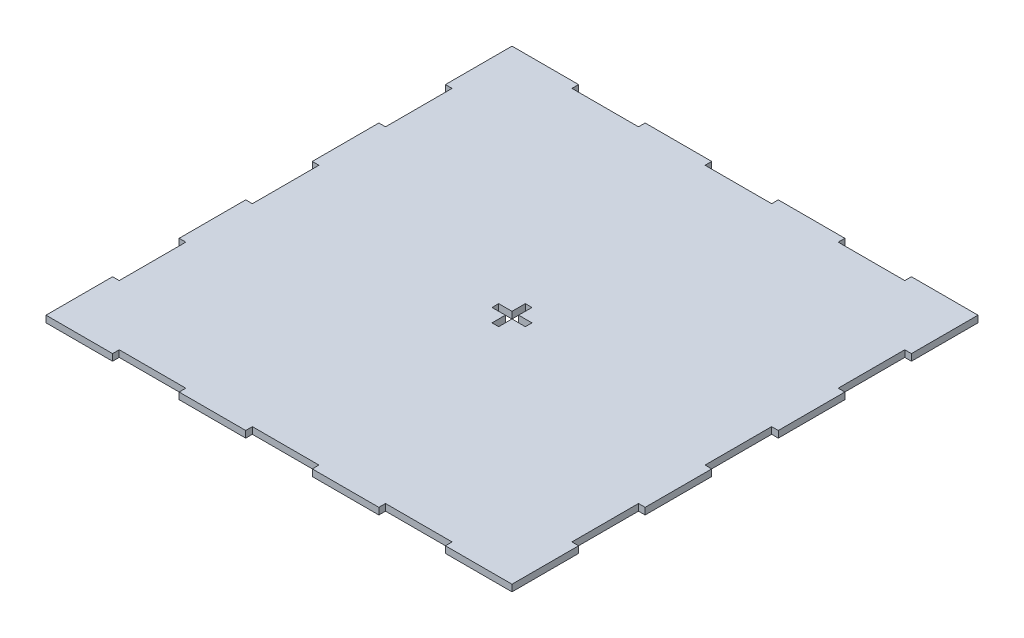
SolidWorks part; units mm, degrees
ref_plane "Front Plane" through (0, 0, 0) normal (0, 0, 1) x (1, 0, 0)
ref_plane "Top Plane" through (0, 0, 0) normal (0, 1, 0) x (1, 0, 0)
ref_plane "Right Plane" through (0, 0, 0) normal (1, 0, 0) x (0, 0, -1)
sketch "Sketch1" plane through (0, 0, 0) normal (0, 1, 0) x (1, 0, 0)
  line L7 (-210, -210) -> (210, -210)
  line L8 (-210, -210) -> (-210, 210)
  line L9 (-210, 210) -> (210, 210)
  line L10 (210, -210) -> (210, 210)
  line L11 (-210, -210) -> (210, 210) construction
  line L12 (-210, 210) -> (210, -210) construction
  point P0 (0, 0)
  dimension "D1" = 420
extrude "Boss-Extrude1" add sketch "Sketch1" along normal blind 6
sketch "Sketch2" plane through (0, 6, 0) normal (0, 1, 0) x (1, 0, 0)
  line L0 (60, 103.923) -> (40, 103.923)
  line L1 (120, 0) -> (60, 103.923) construction
  line L2 (60, 103.923) -> (-60, 103.923) construction
  line L3 (-60, 103.923) -> (-120, 0) construction
  line L4 (-120, 0) -> (-60, -103.923) construction
  line L5 (-60, -103.923) -> (60, -103.923) construction
  line L6 (60, -103.923) -> (120, 0) construction
  line L7 (116.5359, 0) -> (58.2679, 100.923) construction
  line L8 (58.2679, 100.923) -> (-58.2679, 100.923) construction
  line L9 (-58.2679, 100.923) -> (-116.5359, 0) construction
  line L10 (-116.5359, 0) -> (-58.2679, -100.923) construction
  line L11 (-58.2679, -100.923) -> (58.2679, -100.923) construction
  line L12 (58.2679, -100.923) -> (116.5359, 0) construction
  line L13 (40, 103.923) -> (40, 100.923)
  line L14 (40, 100.923) -> (58.2679, 100.923)
  line L15 (58.2679, 100.923) -> (67.4019, 85.1025)
  line L16 (67.4019, 85.1025) -> (70, 86.6025)
  line L17 (70, 86.6025) -> (60, 103.923)
  line L18 (110, -17.3205) -> (120, 0)
  line L19 (120, 0) -> (110, 17.3205)
  line L20 (110, 17.3205) -> (107.4019, 15.8205)
  line L21 (107.4019, 15.8205) -> (116.5359, 0)
  line L22 (116.5359, 0) -> (107.4019, -15.8205)
  line L23 (107.4019, -15.8205) -> (110, -17.3205)
  line L24 (40, -103.923) -> (60, -103.923)
  line L25 (60, -103.923) -> (70, -86.6025)
  line L26 (70, -86.6025) -> (67.4019, -85.1025)
  line L27 (67.4019, -85.1025) -> (58.2679, -100.923)
  line L28 (58.2679, -100.923) -> (40, -100.923)
  line L29 (40, -100.923) -> (40, -103.923)
  line L30 (-70, -86.6025) -> (-60, -103.923)
  line L31 (-60, -103.923) -> (-40, -103.923)
  line L32 (-40, -103.923) -> (-40, -100.923)
  line L33 (-40, -100.923) -> (-58.2679, -100.923)
  line L34 (-58.2679, -100.923) -> (-67.4019, -85.1025)
  line L35 (-67.4019, -85.1025) -> (-70, -86.6025)
  line L36 (-110, 17.3205) -> (-120, 0)
  line L37 (-120, 0) -> (-110, -17.3205)
  line L38 (-110, -17.3205) -> (-107.4019, -15.8205)
  line L39 (-107.4019, -15.8205) -> (-116.5359, 0)
  line L40 (-116.5359, 0) -> (-107.4019, 15.8205)
  line L41 (-107.4019, 15.8205) -> (-110, 17.3205)
  line L42 (-40, 103.923) -> (-60, 103.923)
  line L43 (-60, 103.923) -> (-70, 86.6025)
  line L44 (-70, 86.6025) -> (-67.4019, 85.1025)
  line L45 (-67.4019, 85.1025) -> (-58.2679, 100.923)
  line L46 (-58.2679, 100.923) -> (-40, 100.923)
  line L47 (-40, 100.923) -> (-40, 103.923)
  line L48 (0, 0) -> (130.1568, 75.1461) construction
  line L53 (76.75, 74.9112) -> (78.25, 72.3131)
  line L54 (76.75, 74.9112) -> (90.6757, 82.9512)
  line L55 (78.25, 72.3131) -> (92.1757, 80.3531)
  line L56 (90.6757, 82.9512) -> (92.1757, 80.3531)
  line L57 (74.1519, 73.4112) -> (75.6519, 70.8131)
  line L58 (74.1519, 73.4112) -> (47.3744, 57.9512)
  line L59 (75.6519, 70.8131) -> (48.8744, 55.3531)
  line L60 (47.3744, 57.9512) -> (48.8744, 55.3531)
  line L61 (101.75, 31.6099) -> (115.6757, 39.6499)
  line L62 (117.1757, 37.0519) -> (115.6757, 39.6499)
  line L63 (103.25, 29.0119) -> (117.1757, 37.0519)
  line L64 (103.25, 29.0119) -> (101.75, 31.6099)
  line L65 (99.1519, 30.1099) -> (72.3744, 14.6499)
  line L66 (73.8744, 12.0519) -> (72.3744, 14.6499)
  line L67 (100.6519, 27.5119) -> (73.8744, 12.0519)
  line L68 (100.6519, 27.5119) -> (99.1519, 30.1099)
  line L69 (26.5, -103.923) -> (23.5, -103.923)
  line L70 (26.5, -103.923) -> (26.5, -120.003)
  line L71 (26.5, -120.003) -> (23.5, -120.003)
  line L72 (23.5, -103.923) -> (23.5, -120.003)
  line L73 (26.5, -100.923) -> (23.5, -100.923)
  line L74 (26.5, -100.923) -> (26.5, -70.003)
  line L75 (26.5, -70.003) -> (23.5, -70.003)
  line L76 (23.5, -100.923) -> (23.5, -70.003)
  line L77 (-23.5, -103.923) -> (-23.5, -120.003)
  line L78 (-26.5, -120.003) -> (-23.5, -120.003)
  line L79 (-26.5, -103.923) -> (-26.5, -120.003)
  line L80 (-26.5, -103.923) -> (-23.5, -103.923)
  line L81 (-23.5, -100.923) -> (-23.5, -70.003)
  line L82 (-26.5, -70.003) -> (-23.5, -70.003)
  line L83 (-26.5, -100.923) -> (-26.5, -70.003)
  line L84 (-26.5, -100.923) -> (-23.5, -100.923)
  line L85 (-103.25, 29.0119) -> (-101.75, 31.6099)
  line L86 (-103.25, 29.0119) -> (-117.1757, 37.0519)
  line L87 (-117.1757, 37.0519) -> (-115.6757, 39.6499)
  line L88 (-101.75, 31.6099) -> (-115.6757, 39.6499)
  line L89 (-100.6519, 27.5119) -> (-99.1519, 30.1099)
  line L90 (-100.6519, 27.5119) -> (-73.8744, 12.0519)
  line L91 (-73.8744, 12.0519) -> (-72.3744, 14.6499)
  line L92 (-99.1519, 30.1099) -> (-72.3744, 14.6499)
  line L93 (-78.25, 72.3131) -> (-92.1757, 80.3531)
  line L94 (-90.6757, 82.9512) -> (-92.1757, 80.3531)
  line L95 (-76.75, 74.9112) -> (-90.6757, 82.9512)
  line L96 (-76.75, 74.9112) -> (-78.25, 72.3131)
  line L97 (-75.6519, 70.8131) -> (-48.8744, 55.3531)
  line L98 (-47.3744, 57.9512) -> (-48.8744, 55.3531)
  line L99 (-74.1519, 73.4112) -> (-47.3744, 57.9512)
  line L100 (-74.1519, 73.4112) -> (-75.6519, 70.8131)
  circle A0 centre (0, 0) radius 103.923 construction
  circle A1 centre (0, 0) radius 100.923 construction
  point P1 (90, 51.9615)
  point P52 (0, 0)
  point P69 (48.1244, 56.6522)
  point P104 (0, 0)
  dimension "D1" = 120
  dimension "D2" = 3
  dimension "D3" = 20
  dimension "D5" = 3
  dimension "D6" = 25
  dimension "D7" = 16.08
  dimension "D8" = 30.92
  dimension "D4" = 6
  dimension "D9" = 3
extrude "Cut-Extrude1" [suppressed] cut sketch "Sketch2" against normal through all
sketch "Sketch3" plane through (0, 6, 0) normal (0, 1, 0) x (1, 0, 0)
  line L7 (210, 210) -> (-210, 210) construction
  line L8 (-204, 204) -> (204, 204) construction
  line L9 (-204, 204) -> (-204, -204) construction
  line L10 (-204, -204) -> (204, -204) construction
  line L11 (204, 204) -> (204, -204) construction
  line L12 (-210, 210) -> (-210, -210) construction
  line L14 (-210, -210) -> (210, -210) construction
  line L16 (-204, 150) -> (-210, 150)
  line L17 (-204, 150) -> (-204, 90)
  line L18 (-204, 90) -> (-210, 90)
  line L19 (-210, 150) -> (-210, 90)
  line L105 (-204, 30) -> (-204, -30)
  line L106 (-204, 30) -> (-210, 30)
  line L107 (-210, 30) -> (-210, -30)
  line L108 (-204, -30) -> (-210, -30)
  line L109 (-204, -90) -> (-204, -150)
  line L110 (-204, -90) -> (-210, -90)
  line L111 (-210, -90) -> (-210, -150)
  line L112 (-204, -150) -> (-210, -150)
  line L113 (150, 204) -> (90, 204)
  line L114 (150, 204) -> (150, 210)
  line L115 (150, 210) -> (90, 210)
  line L116 (90, 204) -> (90, 210)
  line L117 (30, 204) -> (-30, 204)
  line L118 (-30, 204) -> (-30, 210)
  line L119 (30, 210) -> (-30, 210)
  line L120 (30, 204) -> (30, 210)
  line L121 (-90, 204) -> (-150, 204)
  line L122 (-150, 204) -> (-150, 210)
  line L123 (-90, 210) -> (-150, 210)
  line L124 (-90, 204) -> (-90, 210)
  line L125 (204, -150) -> (204, -90)
  line L126 (204, -150) -> (210, -150)
  line L127 (210, -150) -> (210, -90)
  line L128 (204, -90) -> (210, -90)
  line L129 (204, -30) -> (204, 30)
  line L130 (204, 30) -> (210, 30)
  line L131 (210, -30) -> (210, 30)
  line L132 (204, -30) -> (210, -30)
  line L133 (204, 90) -> (204, 150)
  line L134 (204, 150) -> (210, 150)
  line L135 (210, 90) -> (210, 150)
  line L136 (204, 90) -> (210, 90)
  line L137 (-150, -204) -> (-90, -204)
  line L138 (-150, -204) -> (-150, -210)
  line L139 (-150, -210) -> (-90, -210)
  line L140 (-90, -204) -> (-90, -210)
  line L141 (-30, -204) -> (30, -204)
  line L142 (30, -204) -> (30, -210)
  line L143 (-30, -210) -> (30, -210)
  line L144 (-30, -204) -> (-30, -210)
  line L145 (90, -204) -> (150, -204)
  line L146 (150, -204) -> (150, -210)
  line L147 (90, -210) -> (150, -210)
  line L148 (90, -204) -> (90, -210)
  point P20 (0, -204)
  point P23 (0, -210)
  point P63 (0, 0)
  dimension "D1" = 6
  dimension "D2" = 6
  dimension "D3" = 60
  dimension "D4" = 60
  dimension "D5" = 3
extrude "Cut-Extrude2" cut sketch "Sketch3" against normal through all
sketch "Sketch4" [suppressed] plane through (0, 5, 0) normal (0, 1, 0) x (1, 0, 0)
  line L0 (-170, -125) -> (-170, -75) construction
  line L1 (-170, -52) -> (-99, -52)
  line L2 (-170, -52) -> (-170, -148)
  line L3 (-170, -148) -> (-99, -148)
  line L4 (-99, -52) -> (-99, -148)
  line L26 (99, -52) -> (99, -148)
  line L27 (99, -52) -> (170, -52)
  line L28 (170, -52) -> (170, -148)
  line L29 (99, -148) -> (170, -148)
  line L30 (99, 48) -> (99, -48)
  line L31 (99, 48) -> (170, 48)
  line L32 (170, 48) -> (170, -48)
  line L33 (99, -48) -> (170, -48)
  line L34 (99, 148) -> (99, 52)
  line L35 (99, 148) -> (170, 148)
  line L36 (170, 148) -> (170, 52)
  line L37 (99, 52) -> (170, 52)
  line L38 (-170, 48) -> (-170, -48)
  line L39 (-170, 48) -> (-99, 48)
  line L40 (-99, 48) -> (-99, -48)
  line L41 (-170, -48) -> (-99, -48)
  line L42 (-170, 148) -> (-170, 52)
  line L43 (-170, 148) -> (-99, 148)
  line L44 (-99, 148) -> (-99, 52)
  line L45 (-170, 52) -> (-99, 52)
  point P6 (-99, 0)
  dimension "D1" = 71
  dimension "D2" = 96
  dimension "D3" = 2
  dimension "D4" = 3
sketch "Sketch5" plane through (0, 6, 0) normal (0, 1, 0) x (1, 0, 0)
  line L0 (3, 3) -> (15, 3)
  line L1 (-15, -3) -> (-3, -3)
  line L2 (-15, -3) -> (-15, 3)
  line L3 (-15, 3) -> (-3, 3)
  line L4 (15, -3) -> (15, 3)
  line L5 (-3, 3) -> (-3, 15)
  line L6 (3, 3) -> (3, 15)
  line L7 (-3, -15) -> (3, -15)
  line L8 (-3, -15) -> (-3, -3)
  line L9 (-3, 15) -> (3, 15)
  line L10 (3, -15) -> (3, -3)
  line L15 (3, -3) -> (15, -3)
  point P0 (0, 0)
  point P6 (0, 0)
  point P11 (0, 15)
  point P14 (-15, 0)
  dimension "D1" = 6
  dimension "D2" = 30
extrude "Cut-Extrude3" cut sketch "Sketch5" against normal through all
sketch "Sketch6" [suppressed] plane through (0, 6, 0) normal (0, 1, 0) x (1, 0, 0)
  line L1 (0, -83.7158) -> (72.5, 41.8579) construction
  line L2 (72.5, 41.8579) -> (-72.5, 41.8579) construction
  line L3 (-72.5, 41.8579) -> (0, -83.7158) construction
  circle A0 centre (0, 0) radius 41.8579 construction
  circle A1 centre (-72.5, 41.8579) radius 7.5
  circle A2 centre (72.5, 41.8579) radius 7.5
  circle A3 centre (0, -83.7158) radius 7.5
  dimension "D2" = 15
  dimension "D1" = 145
extrude "Cut-Extrude4" [suppressed] cut sketch "Sketch6" against normal through all
sketch "Sketch7" [suppressed] plane through (0, 6, 0) normal (0, 1, 0) x (1, 0, 0)
  line L0 (35.391, -18.701) -> (52.7115, -28.701)
  line L1 (-1.5, 40) -> (1.5, 40)
  line L2 (-1.5, 40) -> (-1.5, 60)
  line L3 (-1.5, 60) -> (1.5, 60)
  line L4 (1.5, 40) -> (1.5, 60)
  line L5 (-1.5, 40) -> (1.5, 60) construction
  line L6 (-1.5, 60) -> (1.5, 40) construction
  line L7 (35.391, -18.701) -> (33.891, -21.299)
  line L8 (33.891, -21.299) -> (51.2115, -31.299)
  line L9 (52.7115, -28.701) -> (51.2115, -31.299)
  line L10 (-33.891, -21.299) -> (-51.2115, -31.299)
  line L11 (-33.891, -21.299) -> (-35.391, -18.701)
  line L12 (-35.391, -18.701) -> (-52.7115, -28.701)
  line L13 (-51.2115, -31.299) -> (-52.7115, -28.701)
  point P0 (0, 50)
  point P17 (0, 0)
  dimension "D1" = 3
  dimension "D2" = 20
  dimension "D3" = 50
  dimension "D4" = 3
extrude "Cut-Extrude5" [suppressed] cut sketch "Sketch7" against normal through all
sketch "Sketch8" [suppressed] plane through (0, 6, 0) normal (0, 1, 0) x (1, 0, 0)
  line L0 (0, 0) -> (-60, 103.923) construction
  line L1 (-67.4019, 85.1025) -> (-58.2679, 100.923) construction
  circle A0 centre (-49.6077, 85.923) radius 7.5
  circle A2 centre (49.6077, 85.923) radius 7.5
  circle A3 centre (99.2154, 0) radius 7.5
  circle A4 centre (49.6077, -85.923) radius 7.5
  circle A5 centre (-49.6077, -85.923) radius 7.5
  circle A6 centre (-99.2154, 0) radius 7.5
  point P22 (0, 0)
  dimension "D1" = 15
  dimension "D2" = 15
  dimension "D3" = 6
extrude "Cut-Extrude6" [suppressed] cut sketch "Sketch8" against normal through all
